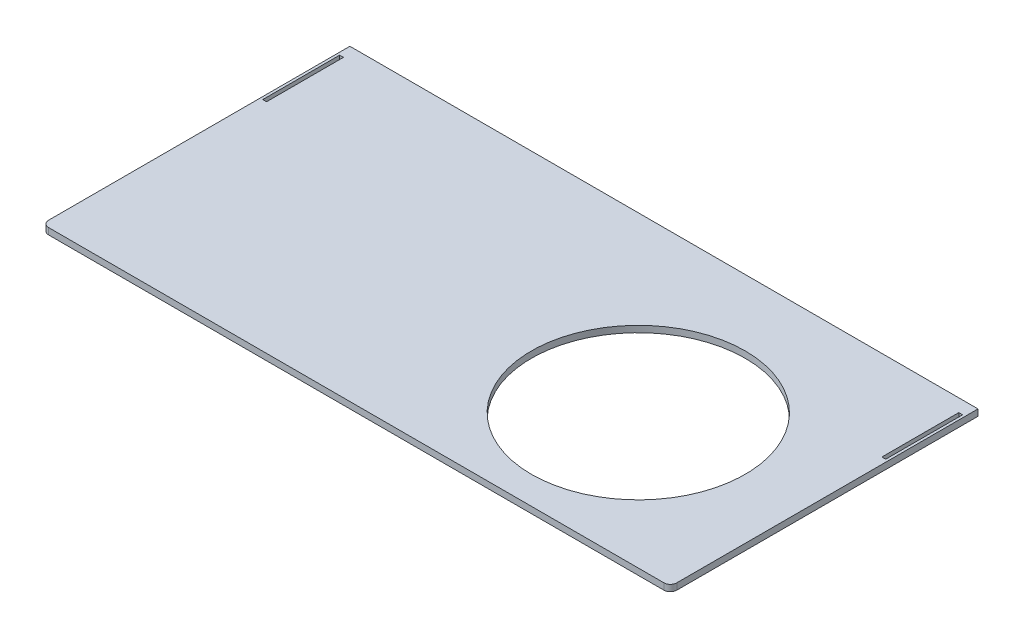
SolidWorks part; units mm, degrees
ref_plane "Alzado" through (0, 0, 0) normal (0, 0, 1) x (1, 0, 0)
ref_plane "Planta" through (0, 0, 0) normal (0, 1, 0) x (1, 0, 0)
ref_plane "Vista lateral" through (0, 0, 0) normal (1, 0, 0) x (0, 0, -1)
sketch "Croquis2" plane through (0, 0, 0) normal (0, 1, 0) x (1, 0, 0)
  line L1 (-311.15, 152.4) -> (311.15, 152.4)
  line L2 (-311.15, 152.4) -> (-311.15, -152.4)
  line L3 (-311.15, -152.4) -> (311.15, -152.4)
  line L4 (311.15, 152.4) -> (311.15, -152.4)
  line L5 (-311.15, 152.4) -> (311.15, -152.4) construction
  line L6 (-311.15, -152.4) -> (311.15, 152.4) construction
  point P0 (0, 0)
  dimension "D1" = 622.3
  dimension "D2" = 304.8
extrude "Saliente-Extruir1" add sketch "Croquis2" along normal blind 6.35
fillet "Redondeo1" radius 6.35 2 edges at (311.15, 3.175, 152.4) (-311.15, 3.175, 152.4)
sketch "Croquis4" plane through (0, 6.35, 0) normal (0, 1, 0) x (1, 0, 0)
  line L0 (311.15, 152.4) -> (-311.15, 152.4) construction
  line L1 (-308.61, 63.5) -> (-304.8, 63.5)
  line L2 (-308.61, 63.5) -> (-308.61, 139.7)
  line L3 (-308.61, 139.7) -> (-304.8, 139.7)
  line L4 (-304.8, 63.5) -> (-304.8, 139.7)
  line L5 (-311.15, 152.4) -> (-311.15, -146.05) construction
  line L6 (0, 0) -> (0, 152.4) construction
  line L7 (308.61, 139.7) -> (304.8, 139.7)
  line L8 (304.8, 63.5) -> (304.8, 139.7)
  line L9 (308.61, 63.5) -> (304.8, 63.5)
  line L10 (308.61, 63.5) -> (308.61, 139.7)
  dimension "D1" = 76.2
  dimension "D2" = 3.81
  dimension "D3" = 12.7
  dimension "D4" = 2.54
extrude "Cortar-Extruir2" cut sketch "Croquis4" against normal through all
sketch "Croquis5" plane through (0, 6.35, 0) normal (0, 1, 0) x (1, 0, 0)
  line L0 (304.8, -152.4) -> (318.6966, -152.4) construction
  line L2 (311.15, -152.4) -> (311.15, -19.05) construction
  line L3 (311.15, -146.05) -> (311.15, 152.4) construction
  line L5 (311.15, -19.05) -> (247.65, -19.05) construction
  line L7 (247.65, -19.05) -> (146.05, -19.05) construction
  circle A1 centre (146.05, -19.05) radius 105.918
  dimension "D3" = 101.6
  dimension "D4" = 211.836
  dimension "D1" = 133.35
  dimension "D2" = 63.5
extrude "Cortar-Extruir3" cut sketch "Croquis5" against normal through all
